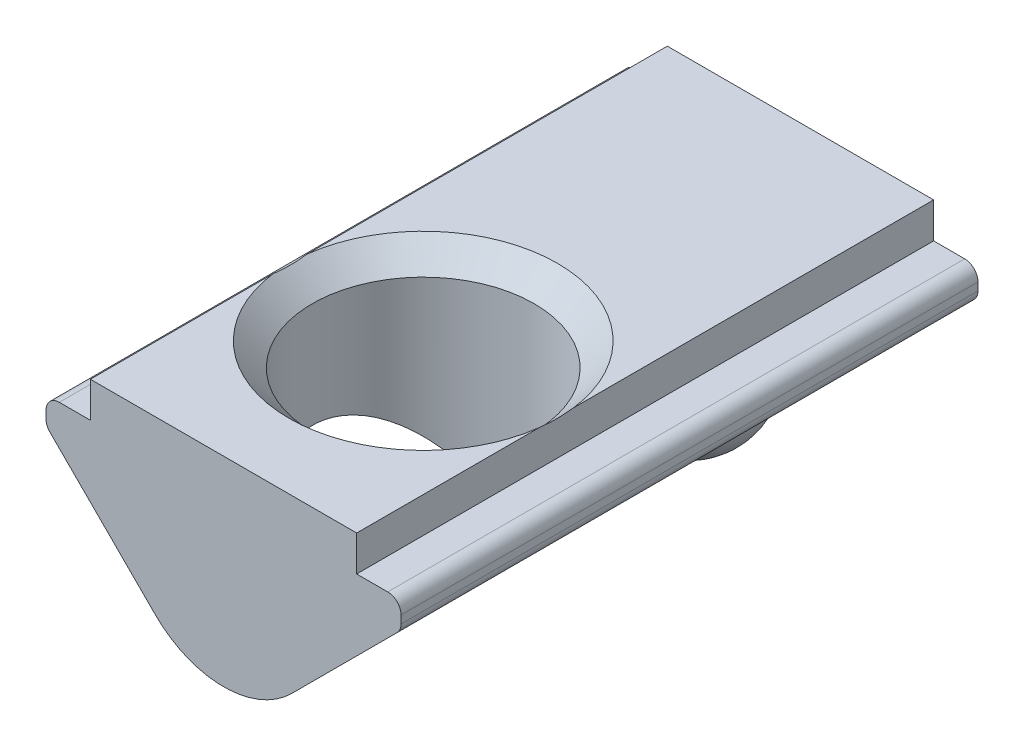
SolidWorks part; units mm, degrees
ref_plane "Спереди" through (0, 0, 0) normal (0, 0, 1) x (1, 0, 0)
ref_plane "Сверху" through (0, 0, 0) normal (0, 1, 0) x (1, 0, 0)
ref_plane "Справа" through (0, 0, 0) normal (1, 0, 0) x (0, 0, -1)
sketch "Эскиз1" plane through (0, 0, 0) normal (0, 0, 1) x (1, 0, 0)
  line L0 (-3, 0) -> (3, 0)
  line L2 (4, -1.4) -> (1.5364, -3.8636)
  line L3 (-1.5364, -3.8636) -> (-4, -1.4)
  line L5 (-3, 0) -> (-3, -0.8)
  line L6 (-3, -0.8) -> (-4, -0.8)
  line L7 (-4, -0.8) -> (-4, -1.4)
  line L8 (3, 0) -> (3, -0.8)
  line L9 (3, -0.8) -> (4, -0.8)
  line L10 (4, -0.8) -> (4, -1.4)
  arc A0 (1.5364, -3.8636) -> (-1.5364, -3.8636) centre (0, -2.3272) cw
  point P4 (0, 0)
  point P6 (-4, -1.8735)
  point P9 (3.8192, -0.8723)
  point P16 (4, -0.8)
  point P17 (4, -0.8)
  point P18 (4, -1.7542)
  point P19 (-2.142, -3.1262)
  dimension "D1" = 6
  dimension "D2" = 8
  dimension "D3" = 0.8
  dimension "D4" = 45
  dimension "D5" = 0.6
  dimension "D6" = 4.5
extrude "Бобышка-Вытянуть1" add sketch "Эскиз1" along normal mid plane 13
hole_wizard "Отверстие обработанное метчиком M61" positions "Эскиз2" profile "Эскиз4" tap size "M6" standard "ISO" end condition through all
sketch "Эскиз2" plane through (0, 0, 0) normal (0, 1, 0) x (1, 0, 0)
  line L0 (3, -6.5) -> (-3, -6.5) construction
  point P0 (0, -2)
  dimension "D1" = 4.5
sketch "Эскиз4" plane through (0, 0, 2) normal (1, 0, 0) x (0, 0, 1)
  line L0 (0, 0) -> (0, 4.5)
  line L1 (0, 4.5) -> (2.5, 4.5)
  line L2 (2.5, 4.5) -> (2.5, 0.525)
  line L3 (2.5, 0.525) -> (3.025, 0)
  line L5 (3.025, 0) -> (0, 0)
  line L6 (-2.5, 0.525) -> (-3.025, 0) construction
  line L11 (0, -6.35) -> (0, 107.95) construction
  dimension "Диаметр проходного сверла" = 5
  dimension "Глубина проходного сверла" = 4.5
  dimension "Диаметр передней зенковки" = 6.05
  dimension "Угол передней зенковки" = 90
cosmetic thread "Отверстие резьбы1" parameters "D2"=6
sketch "Эскиз5" plane through (0, 0, 0) normal (1, 0, 0) x (0, 0, -1)
  line L0 (-6.5, 0) -> (-2.3881, 0) construction
  line L1 (4, -2) -> (4, -5) construction
  line L2 (6.5, -3.8636) -> (6.5, -1.4) construction
  line L3 (4, -2) -> (4, -5)
  arc A0 (4, -2) -> (4, -5) centre (4, -3.5) ccw
  point P3 (0, 0)
  dimension "D3" = 1.5
  dimension "D1" = 5
  dimension "D2" = 2.5
revolve "Повернуть1" add sketch "Эскиз5" angle 360 about L1
fillet "Скругление1" radius 0.3 4 edges at (4, -1.4, 0) (4, -0.8, 0) (-4, -0.8, 0) (-4, -1.4, 0)
